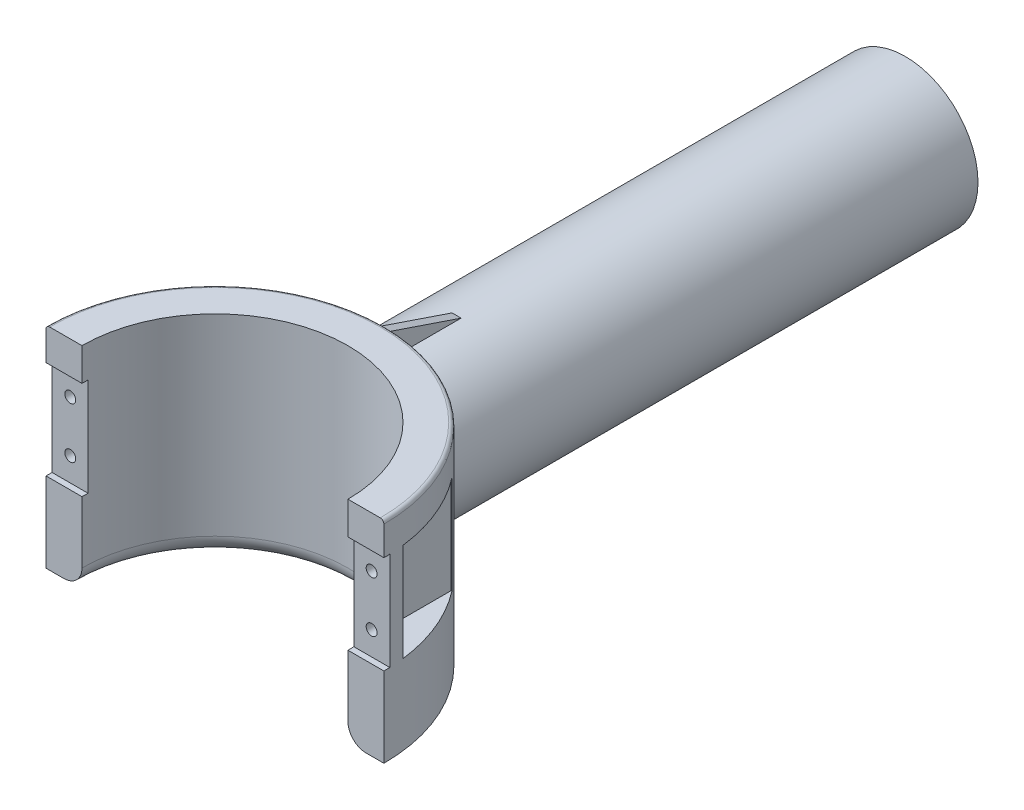
SolidWorks part; units mm, degrees
ref_plane "前视基准面" through (0, 0, 0) normal (0, 0, 1) x (1, 0, 0)
ref_plane "上视基准面" through (0, 0, 0) normal (0, 1, 0) x (1, 0, 0)
ref_plane "右视基准面" through (0, 0, 0) normal (1, 0, 0) x (0, 0, -1)
sketch "草图1" plane through (0, 0, 0) normal (0, 1, 0) x (1, 0, 0)
  line L0 (-46.5, 0) -> (-36.6, 0)
  line L1 (36.6, 0) -> (46.5, 0)
  arc A0 (46.5, 0) -> (-46.5, 0) centre (0, 0) ccw
  arc A1 (36.6, 0) -> (-36.6, 0) centre (0, 0) ccw
  dimension "D1" = 73.2
  dimension "D2" = 93
extrude "凸台-拉伸1" add sketch "草图1" along normal blind 58
fillet "圆角1" radius 5 1 edges at (0, 0, -36.6)
sketch "草图2" plane through (0, 0, 0) normal (0, 0, 1) x (1, 0, 0)
  line L6 (-46.5, 58) -> (-36.6, 58) construction
  line L7 (-48.2491, 22) -> (-34.0507, 22)
  line L8 (-48.2491, 22) -> (-48.2491, 49)
  line L9 (-48.2491, 49) -> (-34.0507, 49)
  line L10 (-34.0507, 22) -> (-34.0507, 49)
  dimension "D1" = 9
  dimension "D2" = 27
extrude "切除-拉伸1" cut sketch "草图2" against normal blind 1.65
sketch "草图3" plane through (0, 0, -1.65) normal (0, 0, 1) x (1, 0, 0)
  line L0 (-46.4707, 22) -> (-46.4707, 49) construction
  line L1 (-46.5, 49) -> (-36.6, 49) construction
  circle A0 centre (-41.4707, 28.5) radius 1.5
  circle A1 centre (-41.4707, 42.5) radius 1.5
  dimension "D1" = 5
  dimension "D2" = 3
  dimension "D5" = 5
  dimension "D3" = 6.5
  dimension "D4" = 14
extrude "切除-拉伸2" cut sketch "草图3" against normal up to next
sketch "草图4" plane through (0, 0, -1.65) normal (0, 0, 1) x (1, 0, 0)
  line L1 (-46.5, 22) -> (-36.6, 22)
  line L2 (-46.5, 22) -> (-46.5, 49)
  line L3 (-46.5, 49) -> (-36.6, 49)
  line L4 (-36.6, 22) -> (-36.6, 49)
ref_plane "基准面1" through (0, 0, -5.65) normal (0, 0, 1) x (1, 0, 0)
sketch "草图5" plane through (0, 0, -5.65) normal (0, 0, 1) x (1, 0, 0)
  line L1 (-46.5, 22) -> (-36.6, 22)
  line L2 (-46.5, 22) -> (-46.5, 49)
  line L3 (-46.5, 49) -> (-36.6, 49)
  line L4 (-36.6, 22) -> (-36.6, 49)
extrude "切除-拉伸3" cut sketch "草图5" against normal blind 22.65
mirror "镜向2" about plane through (0, 0, 0) normal (1, 0, 0) of "切除-拉伸1", "切除-拉伸2", "切除-拉伸3"
ref_plane "基准面2" through (0, 0, -40) normal (0, 0, 1) x (1, 0, 0)
sketch "草图7" plane through (0, 0, -40) normal (0, 0, 1) x (1, 0, 0)
  circle A0 centre (0, 30.2279) radius 20
  dimension "D1" = 40
extrude "凸台-拉伸2" add sketch "草图7" against normal blind 150
sketch "草图9" plane through (0, 0, 0) normal (0, 1, 0) x (1, 0, 0)
  line L1 (18, 67.2638) -> (-18, 67.2638)
  line L2 (18, 67.2638) -> (18, 99.2638)
  line L3 (18, 99.2638) -> (-18, 99.2638)
  line L4 (-18, 67.2638) -> (-18, 99.2638)
  line L5 (18, 67.2638) -> (-18, 99.2638) construction
  line L6 (18, 99.2638) -> (-18, 67.2638) construction
  point P0 (0, 83.2638)
  dimension "D1" = 32
  dimension "D2" = 36
  dimension "D3" = 0
extrude "切除-拉伸5" cut sketch "草图9" against normal blind 8 from offset 15
sketch "草图10" plane through (0, 0, 0) normal (0, -1, 0) x (1, 0, 0)
  line L0 (0, 0) -> (-30.1641, -41.5173) construction
  line L1 (-46.5, 0) -> (-41.6, 0) construction
  line L2 (0, 0) -> (0, 24.8537) construction
  circle A0 centre (0, 0) radius 44.5 construction
  circle A1 centre (-26.1564, -36.0013) radius 1
  circle A2 centre (26.1564, -36.0013) radius 1
  dimension "D1" = 89
  dimension "D3" = 2
  dimension "D2" = 54
extrude "切除-拉伸6" cut sketch "草图10" against normal blind 2
fillet "圆角2" radius 1 1 edges at (0, 58, -46.5)
sketch "草图11" plane through (0, 0, 0) normal (1, 0, 0) x (0, 0, -1)
  line L0 (46.5, 50.2279) -> (46.5, 57)
  line L1 (46.5, 57) -> (66.5, 50.2279)
  line L2 (190, 50.2279) -> (46.5, 50.2279) construction
  line L3 (66.5, 50.2279) -> (46.5, 50.2279)
  dimension "D1" = 20
extrude "凸台-拉伸3" add sketch "草图11" along normal mid plane 2.5 separate body
